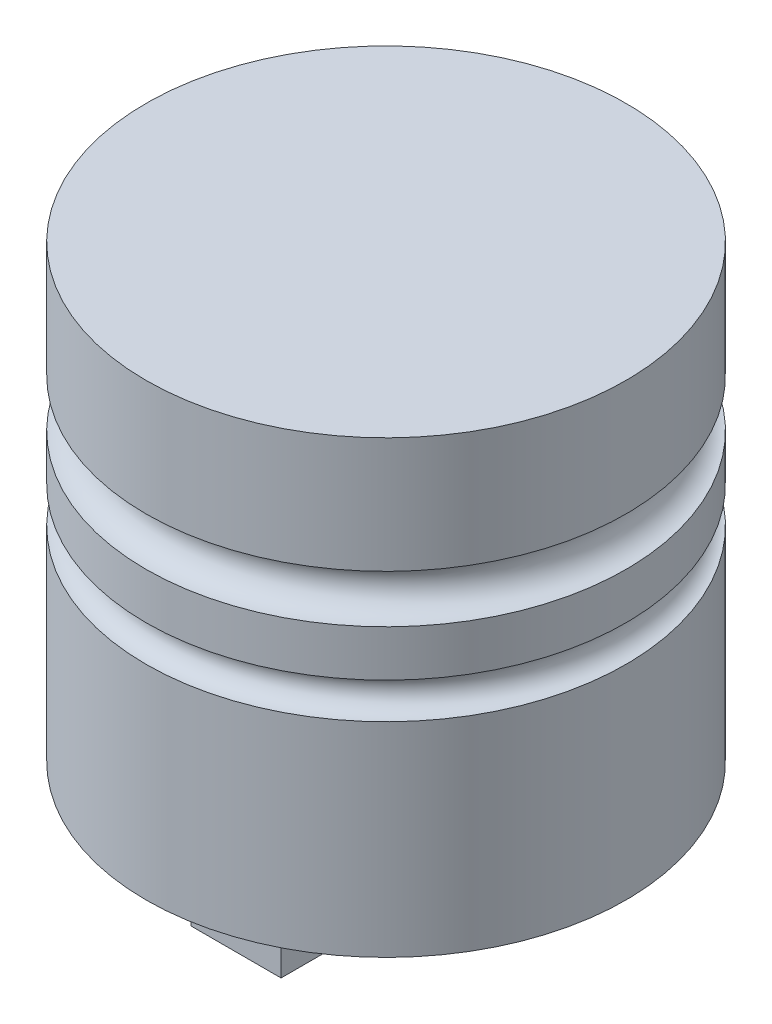
SolidWorks part; units mm, degrees
ref_plane "Front Plane" through (0, 0, 0) normal (0, 0, 1) x (1, 0, 0)
ref_plane "Top Plane" through (0, 0, 0) normal (0, 1, 0) x (1, 0, 0)
ref_plane "Right Plane" through (0, 0, 0) normal (1, 0, 0) x (0, 0, -1)
sketch "Sketch1" plane through (0, 0, 0) normal (0, 0, 1) x (1, 0, 0)
  line L0 (0, 74.6021) -> (0, -75.3979) construction
  line L1 (0, 74.6021) -> (0, -75.3979)
  line L2 (0, 74.6021) -> (80, 74.6021)
  line L3 (0, -75.3979) -> (80, -75.3979)
  line L4 (80, 74.6021) -> (80, 36.0504)
  line L5 (80, 20.0504) -> (80, 4.6393)
  line L6 (80, -7.3607) -> (80, -75.3979)
  line L7 (0, -134.2291) -> (0, 141.6389) construction
  arc A0 (80, 36.0504) -> (80, 20.0504) centre (80, 28.0504) ccw
  arc A1 (80, 4.6393) -> (80, -7.3607) centre (80, -1.3607) ccw
  dimension "D3" = 8
  dimension "D4" = 6
  dimension "D1" = 150
  dimension "D2" = 80
revolve "Revolve1" add sketch "Sketch1" angle 360 about L0
sketch "Sketch3" plane through (0, -75.3979, 0) normal (0, -1, 0) x (1, 0, 0)
  line L0 (0, 80) -> (0, 20) construction
  line L1 (15, -20) -> (15, -50)
  line L2 (-15, 50) -> (15, 50)
  line L3 (-15, 50) -> (-15, 20)
  line L4 (-15, -50) -> (15, -50)
  line L5 (15, 50) -> (15, 20)
  line L6 (-15, 50) -> (-6, 20) construction
  line L7 (-15, -50) -> (-6, -20) construction
  line L8 (15, -20) -> (-15, -20)
  line L9 (80, 0) -> (-80, 0) construction
  line L10 (15, 20) -> (-15, 20)
  line L14 (6, -20) -> (15, -50) construction
  line L15 (0, -20) -> (0, -80) construction
  line L16 (6, 20) -> (15, 50) construction
  line L17 (-15, -20) -> (-15, -50)
  circle A0 centre (0, 0) radius 80 construction
  point P5 (0, 0)
  point P10 (0, 0)
  dimension "D1" = 30
  dimension "D2" = 30
  dimension "D3" = 40
  dimension "D4" = 20
  dimension "D5" = 15
extrude "Boss-Extrude1" add sketch "Sketch3" along normal blind 30
sketch "Sketch4" plane through (0, 0, 20) normal (0, 0, -1) x (-1, 0, 0)
  line L0 (-15, -75.3979) -> (15, -105.3979) construction
  line L1 (-15, -105.3979) -> (15, -75.3979) construction
  circle A0 centre (0, -90.3979) radius 10
  dimension "D1" = 20
extrude "Boss-Extrude2" add sketch "Sketch4" along normal up to surface (40 mm away) contours A0 up to face at (0, -90.3979, -20)
